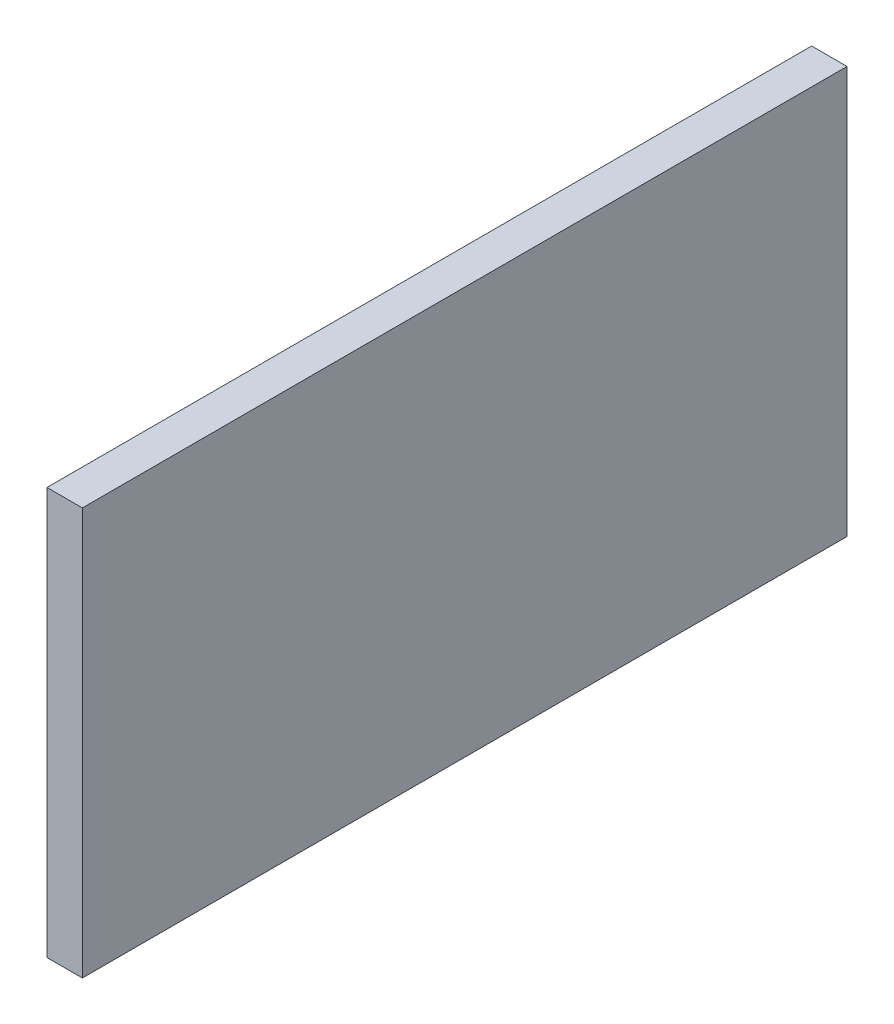
SolidWorks part; units mm, degrees
material "POLYURETHANE (11671)"
ref_plane "Front Plane" through (0, 0, 0) normal (0, 0, 1) x (1, 0, 0)
ref_plane "Top Plane" through (0, 0, 0) normal (0, 1, 0) x (1, 0, 0)
ref_plane "Right Plane" through (0, 0, 0) normal (1, 0, 0) x (0, 0, -1)
sketch "Sketch1" plane through (0, 0, 0) normal (1, 0, 0) x (0, 0, -1)
  line L1 (-34.29, -18.2562) -> (34.29, -18.2562)
  line L2 (-34.29, -18.2562) -> (-34.29, 18.2563)
  line L3 (-34.29, 18.2563) -> (34.29, 18.2563)
  line L4 (34.29, -18.2562) -> (34.29, 18.2563)
  line L5 (-34.29, -18.2562) -> (34.29, 18.2563) construction
  line L6 (-34.29, 18.2563) -> (34.29, -18.2562) construction
  point P0 (0, 0)
  dimension "D1" = 68.58
  dimension "D2" = 36.5125
extrude "Boss-Extrude1" add sketch "Sketch1" along normal blind 3.175
